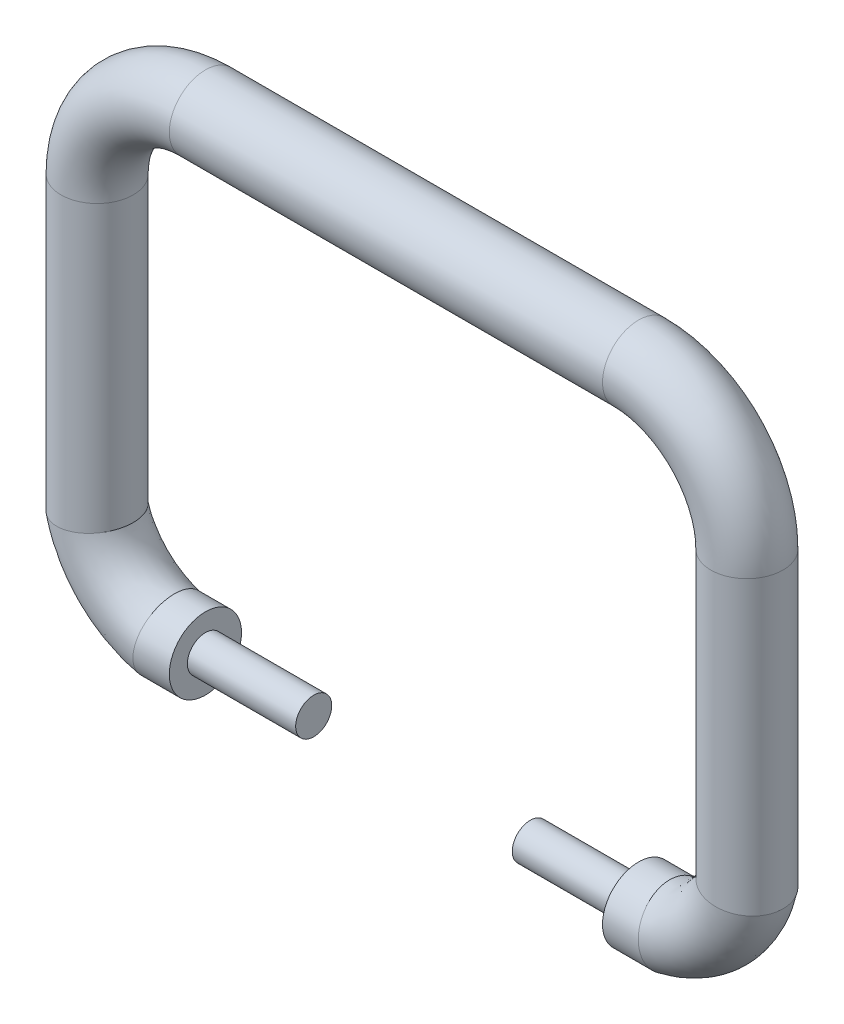
SolidWorks part; units mm, degrees
ref_plane "Front Plane" through (0, 0, 0) normal (0, 0, 1) x (1, 0, 0)
ref_plane "Top Plane" through (0, 0, 0) normal (0, 1, 0) x (1, 0, 0)
ref_plane "Right Plane" through (0, 0, 0) normal (1, 0, 0) x (0, 0, -1)
sketch "Sketch1" plane through (0, 0, 0) normal (0, 0, 1) x (1, 0, 0)
  line L0 (0, 0) -> (-30, 0)
  line L1 (-45, -15) -> (-45, -55)
  line L2 (-35, -65) -> (-15, -65)
  arc A0 (-30, 0) -> (-45, -15) centre (-30, -15) ccw
  arc A1 (-45, -55) -> (-35, -65) centre (-31.5576, -51.5576) ccw
  dimension "D5" = 15
  dimension "D6" = 10
  dimension "D1" = 30
  dimension "D2" = 45
  dimension "D3" = 15
  dimension "D4" = 40
  dimension "D7" = 10
  dimension "D8" = 20
sketch "Sketch2" plane through (0, 0, 0) normal (1, 0, 0) x (0, 0, -1)
  circle A1 centre (0, 0) radius 5
  dimension "D2" = 10
sweep "Sweep1" add profiles "Sketch2" path "Sketch1"
ref_plane "Plane1" through (-52.5, 0, 0) normal (1, 0, 0) x (0, 0, -1)
sketch "Sketch5" plane through (-52.5, 0, 0) normal (1, 0, 0) x (0, 0, -1)
  line L1 (0, 0) -> (0, -45) construction
mirror "Mirror3" about plane through (0, 0, 0) normal (1, 0, 0) of "Sweep1"
sketch "Sketch6" plane through (-15, 0, 0) normal (1, 0, 0) x (0, 0, -1)
  circle A3 centre (0, -65) radius 2.5
  circle A4 centre (0, -65) radius 5 construction
  circle A5 centre (0, -65) radius 7.5
  dimension "D1" = 5
  dimension "D2" = 15
sketch "Sketch7" plane through (15, 0, 0) normal (-1, 0, 0) x (0, 0, 1)
  circle A0 centre (0, -65) radius 2.5
  circle A1 centre (0, -65) radius 5 construction
  circle A2 centre (0, -65) radius 7.5
  dimension "D1" = 5
  dimension "D2" = 15
extrude "Cut-Extrude1" cut sketch "Sketch6" against normal blind 15
extrude "Cut-Extrude2" cut sketch "Sketch7" against normal blind 15
